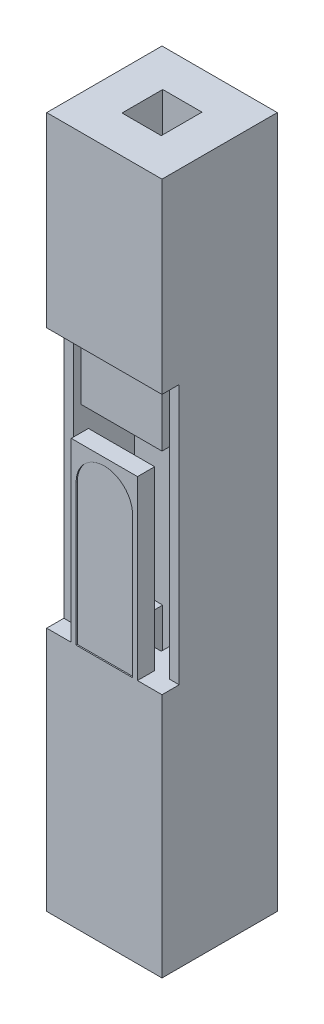
SolidWorks part; units mm, degrees
other "Camera1"
material "Nylon 101"
ref_plane "Front Plane" through (0, 0, 0) normal (0, 0, 1) x (1, 0, 0)
ref_plane "Top Plane" through (0, 0, 0) normal (0, 1, 0) x (1, 0, 0)
ref_plane "Right Plane" through (0, 0, 0) normal (1, 0, 0) x (0, 0, -1)
sketch "Sketch2" plane through (0, 0, 0) normal (0, 1, 0) x (1, 0, 0)
  line L1 (-1.175, -1.175) -> (1.175, -1.175)
  line L2 (-1.175, -1.175) -> (-1.175, 1.175)
  line L3 (-1.175, 1.175) -> (1.175, 1.175)
  line L4 (1.175, -1.175) -> (1.175, 1.175)
  line L5 (-1.175, -1.175) -> (1.175, 1.175) construction
  line L6 (-1.175, 1.175) -> (1.175, -1.175) construction
  point P0 (0, 0)
  dimension "D1" = 2.35
extrude "Boss-Extrude1" add sketch "Sketch2" along normal mid plane 14.1
sketch "Sketch3" plane through (0, 7.05, 0) normal (0, 1, 0) x (1, 0, 0)
  line L1 (0.4, -0.415) -> (-0.4, -0.415)
  line L2 (0.4, -0.415) -> (0.4, 0.415)
  line L3 (0.4, 0.415) -> (-0.4, 0.415)
  line L4 (-0.4, -0.415) -> (-0.4, 0.415)
  line L5 (0.4, -0.415) -> (-0.4, 0.415) construction
  line L6 (0.4, 0.415) -> (-0.4, -0.415) construction
  point P0 (0, 0)
  dimension "D1" = 0.83
  dimension "D2" = 0.8
extrude "Pinhole" cut sketch "Sketch3" against normal up to next
sketch "Sketch4" plane through (0, 0, 1.175) normal (0, 0, 1) x (1, 0, 0)
  line L0 (-1.175, 7.05) -> (-1.175, -7.05) construction
  line L1 (-1.175, 3.25) -> (1.175, 3.25)
  line L2 (-1.175, 3.25) -> (-1.175, -2.05)
  line L3 (-1.175, -2.05) -> (-0.675, -2.05)
  line L4 (1.175, 3.25) -> (1.175, -2.05)
  line L5 (0.675, -2.05) -> (1.175, -2.05)
  line L6 (-0.675, -2.05) -> (0.675, -2.05) construction
  line L7 (1.175, 7.05) -> (1.175, -7.05) construction
  line L8 (-1.175, 7.05) -> (1.175, 7.05) construction
  line L9 (-1.175, -7.05) -> (1.175, -7.05) construction
  line L10 (-0.675, -2.05) -> (-0.675, 1.55)
  line L11 (-0.675, 1.55) -> (0.675, 1.55)
  line L12 (0.675, -2.05) -> (0.675, 1.55)
  dimension "D1" = 3.8
  dimension "D2" = 5
  dimension "D3" = 1.35
  dimension "D4" = 3.6
extrude "Cut-Extrude2" cut sketch "Sketch4" against normal blind 0.35
sketch "Sketch5" plane through (0, 0, 0.825) normal (0, 0, 1) x (1, 0, 0)
  line L0 (-1.175, 7.05) -> (1.175, 7.05) construction
  line L1 (-0.975, 3.25) -> (0.975, 3.25)
  line L2 (-0.975, 3.25) -> (-0.975, -2.05)
  line L3 (-0.975, -2.05) -> (0.975, -2.05)
  line L4 (0.975, 3.25) -> (0.975, -2.05)
  line L5 (-0.975, 3.25) -> (0.975, -2.05) construction
  line L6 (-0.975, -2.05) -> (0.975, 3.25) construction
  line L7 (0.675, -2.05) -> (1.175, -2.05) construction
  line L8 (-1.175, 3.25) -> (-1.175, -2.05) construction
  line L9 (1.175, 3.25) -> (-1.175, 3.25) construction
  point P4 (0, 0.6)
  point P5 (0, 3.25)
  point P8 (0, 7.05)
  dimension "D1" = 0.2
extrude "Cut-Extrude3" cut sketch "Sketch5" against normal up to surface (1.24 mm away) up to face at (0, 0, -0.415)
sketch "Sketch6" plane through (0, 0, 1.175) normal (0, 0, 1) x (1, 0, 0)
  line L0 (-0.575, -2.05) -> (-0.575, 0.825)
  line L1 (-0.675, -2.05) -> (-0.675, 1.55) construction
  line L2 (-0.6875, -2.05) -> (0.6875, -2.05)
  line L3 (-0.975, -2.05) -> (-0.4, -2.05) construction
  line L4 (0.4, -2.05) -> (0.975, -2.05) construction
  line L5 (0, 1.55) -> (0, -2.05) construction
  line L6 (-0.675, 1.55) -> (0.675, 1.55) construction
  line L7 (0.575, -2.05) -> (0.575, 0.825)
  arc A0 (-0.575, 0.825) -> (0.575, 0.825) centre (0, 0.825) cw
  point P17 (0, 1.4)
  dimension "D2" = 0.15
  dimension "D1" = 0.1
extrude "Cut-Extrude5" cut sketch "Sketch6" against normal blind 0.025 contours L5 A0 L0 L2 | A0 L5 L2 L7
sketch "Sketch7" plane through (0, -7.05, 0) normal (0, -1, 0) x (1, 0, 0)
  line L0 (-1.175, -1.175) -> (-1.175, 1.175) construction
  line L1 (0.975, -0.975) -> (-0.975, -0.975)
  line L2 (0.975, -0.975) -> (0.975, 0.975)
  line L3 (0.975, 0.975) -> (-0.975, 0.975)
  line L4 (-0.975, -0.975) -> (-0.975, 0.975)
  line L5 (0.975, -0.975) -> (-0.975, 0.975) construction
  line L6 (0.975, 0.975) -> (-0.975, -0.975) construction
  point P0 (0, 0)
  dimension "D1" = 0.2
extrude "Cut-Extrude6" cut sketch "Sketch7" against normal blind 4
sketch "Sketch8" [suppressed] plane through (0, -3.05, 0) normal (0, -1, 0) x (1, 0, 0)
  circle A0 centre (0, 0) radius 0.45
  circle A1 centre (0, 0) radius 0.55
  dimension "D1" = 0.9
  dimension "D2" = 0.1
extrude "Wire hole" [suppressed] add sketch "Sketch8" along normal blind 3
sketch "Sketch9" plane through (0, 0, -0.415) normal (0, 0, 1) x (1, 0, 0)
  line L1 (-0.825, 2.9) -> (-0.675, 2.9)
  line L2 (-0.825, 2.9) -> (-0.825, 1.9)
  line L3 (-0.825, 1.9) -> (-0.675, 1.9)
  line L4 (0.825, 2.9) -> (0.825, 1.9)
  line L5 (0.675, 2.9) -> (-0.675, 2.9) construction
  line L6 (0.825, 2.9) -> (0.675, 2.9)
  line L7 (-0.4, 3.25) -> (0.4, 3.25) construction
  line L8 (-0.675, 2.9) -> (-0.675, 1.9)
  line L9 (0, 2.9) -> (0, 1.9) construction
  line L10 (0.675, 2.9) -> (0.675, 1.9)
  line L11 (-0.975, 3.25) -> (-0.975, -2.05) construction
  line L12 (0, 3.25) -> (0, 2.9) construction
  line L13 (0.675, 1.9) -> (-0.675, 1.9) construction
  line L14 (0.675, 1.9) -> (0.825, 1.9)
  point P4 (0, 2.4)
  point P23 (0, 2.9)
  point P24 (0, 1.9)
  dimension "D1" = 1
  dimension "D2" = 0.15
  dimension "D3" = 0.15
  dimension "D4" = 0.85
extrude "Holder-1" add sketch "Sketch9" along normal offset from surface (1.09 mm away) 0.15 up to face at (0, -0.25, 0.825)
sketch "Sketch10" plane through (0, 0, 0.675) normal (0, 0, 1) x (1, 0, 0)
  line L1 (-0.825, 2.9) -> (0.825, 2.9)
  line L2 (-0.825, 2.9) -> (-0.825, 1.9)
  line L3 (-0.825, 1.9) -> (0.825, 1.9)
  line L4 (0.825, 2.9) -> (0.825, 1.9)
  line L5 (-0.825, 2.9) -> (0.825, 1.9) construction
  line L6 (-0.825, 1.9) -> (0.825, 2.9) construction
  point P4 (0, 2.4)
extrude "Holder-2" add sketch "Sketch10" along normal blind 0.15
ref_plane "Snap plane" through (0, 6.05, 0) normal (0, 1, 0) x (1, 0, 0)
